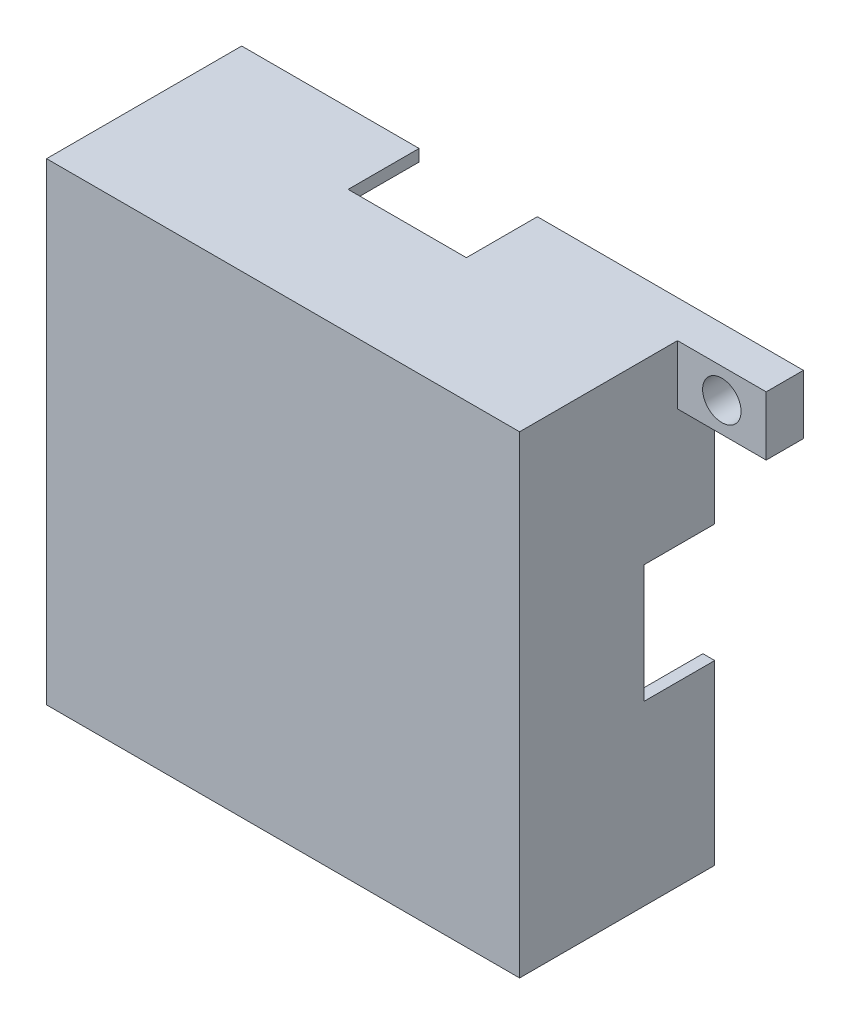
SolidWorks part; units mm, degrees
ref_plane "Front Plane" through (0, 0, 0) normal (0, 0, 1) x (1, 0, 0)
ref_plane "Top Plane" through (0, 0, 0) normal (0, 1, 0) x (1, 0, 0)
ref_plane "Right Plane" through (0, 0, 0) normal (1, 0, 0) x (0, 0, -1)
sketch "Sketch1" plane through (0, 0, 0) normal (0, 0, 1) x (1, 0, 0)
  line L1 (0, 0) -> (40, 0)
  line L2 (0, 0) -> (0, 40)
  line L3 (0, 40) -> (40, 40)
  line L4 (40, 0) -> (40, 40)
  line L5 (1, 1) -> (39, 1)
  line L6 (1, 1) -> (1, 39)
  line L7 (1, 39) -> (39, 39)
  line L8 (39, 1) -> (39, 39)
  dimension "D1" = 1
  dimension "D2" = 1
  dimension "D3" = 1
  dimension "D4" = 1
  dimension "D5" = 40
  dimension "D6" = 40
extrude "Boss-Extrude1" add sketch "Sketch1" along normal blind 15
sketch "Sketch2" plane through (0, 0, 15) normal (0, 0, 1) x (1, 0, 0)
  line L1 (0, 40) -> (40, 40)
  line L2 (0, 40) -> (0, 0)
  line L3 (0, 0) -> (40, 0)
  line L4 (40, 40) -> (40, 0)
extrude "Boss-Extrude2" add sketch "Sketch2" along normal blind 1.5
sketch "Sketch3" plane through (0, 0, 0) normal (0, 0, -1) x (-1, 0, 0)
  line L1 (-40, 40) -> (-47.5, 40)
  line L2 (-40, 40) -> (-40, 35)
  line L3 (-40, 35) -> (-47.5, 35)
  line L4 (-47.5, 40) -> (-47.5, 35)
  circle A0 centre (-43.75, 37.5) radius 1.625
  point P7 (-43.75, 40)
  point P9 (-47.5, 37.5)
  dimension "D3" = 3.25
  dimension "D1" = 7.5
  dimension "D2" = 5
extrude "Boss-Extrude3" add sketch "Sketch3" against normal blind 3.15
sketch "Sketch4" plane through (0, 0, 0) normal (-1, 0, 0) x (0, 0, 1)
  line L0 (0, 40) -> (0, 0) construction
  line L1 (0, 25) -> (6, 25)
  line L2 (0, 25) -> (0, 15)
  line L3 (0, 15) -> (6, 15)
  line L4 (6, 25) -> (6, 15)
  point P6 (0, 20)
  point P7 (0, 20)
  dimension "D1" = 6
  dimension "D2" = 0
  dimension "D3" = 10
extrude "Cut-Extrude1" cut sketch "Sketch4" against normal through all both and the other way through all
sketch "Sketch5" plane through (0, 0, 0) normal (0, -1, 0) x (1, 0, 0)
  line L0 (0, 0) -> (40, 0) construction
  line L1 (15, 0) -> (25, 0)
  line L2 (15, 0) -> (15, 6)
  line L3 (15, 6) -> (25, 6)
  line L4 (25, 0) -> (25, 6)
  point P6 (20, 0)
  point P7 (20, 0)
  dimension "D1" = 10
  dimension "D2" = 6
  dimension "D3" = 0
extrude "Cut-Extrude2" cut sketch "Sketch5" against normal through all both and the other way through all
